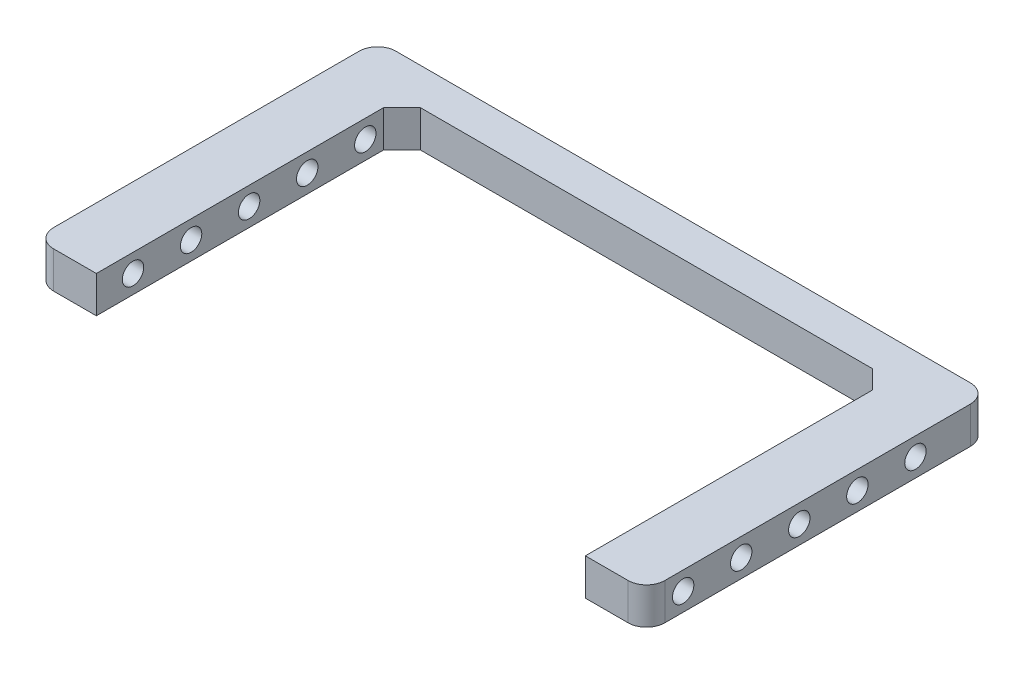
SolidWorks part; units mm, degrees
ref_plane "Front" through (0, 0, 0) normal (0, 0, 1) x (1, 0, 0)
ref_plane "Top" through (0, 0, 0) normal (0, 1, 0) x (1, 0, 0)
ref_plane "Right" through (0, 0, 0) normal (1, 0, 0) x (0, 0, -1)
sketch "Sketch1" plane through (0, 0, 0) normal (0, 1, 0) x (1, 0, 0)
  line L0 (-25, -14) -> (-20, -14)
  line L1 (-25, -14) -> (25, -14) construction
  line L2 (-25, -14) -> (-25, 14)
  line L3 (-25, 14) -> (25, 14)
  line L4 (25, -14) -> (25, 14)
  line L5 (-25, -14) -> (25, 14) construction
  line L6 (-25, 14) -> (25, -14) construction
  line L7 (-20, -14) -> (-20, 11)
  line L8 (-20, 11) -> (20, 11)
  line L9 (20, 11) -> (20, -14)
  line L10 (20, -14) -> (25, -14)
  line L12 (0, 0) -> (0, 11) construction
  point P0 (0, 0)
  dimension "D1" = 40
  dimension "D2" = 25
  dimension "D3" = 3
  dimension "D4" = 5
  dimension "D5" = 5
  dimension "D6" = 11
extrude "Boss-Extrude1" add sketch "Sketch1" along normal blind 3
sketch "Sketch2" plane through (25, 0, 0) normal (-1, 0, 0) x (0, 0, 1)
  line L0 (14, 1.5) -> (11, 1.5) construction
  line L1 (14, 3) -> (14, 0) construction
  line L2 (11, 1.5) -> (6.25, 1.5) construction
  line L3 (-8, 1.5) -> (-11, 1.5) construction
  line L4 (-11, 3) -> (-11, 0) construction
  circle A0 centre (11, 1.5) radius 0.875
  circle A1 centre (6.25, 1.5) radius 0.875
  circle A2 centre (1.5, 1.5) radius 0.875
  circle A3 centre (-3.25, 1.5) radius 0.875
  circle A4 centre (-8, 1.5) radius 0.875
  dimension "D1" = 1.75
  dimension "D2" = 3
  dimension "D3" = 5
extrude "Cut-Extrude1" cut sketch "Sketch2" against normal blind 3 and the other way through all
fillet "Fillet2" radius 1.5 4 edges at (-25, 1.5, -14) (-25, 1.5, 14) (25, 1.5, -14) (25, 1.5, 14)
chamfer "Chamfer1" distance 1.5 angle 45 2 edges at (-20, 1.5, -11) (20, 1.5, -11)
move or copy body "Body-Move/Copy1" [suppressed] bodies to move or copy 104
